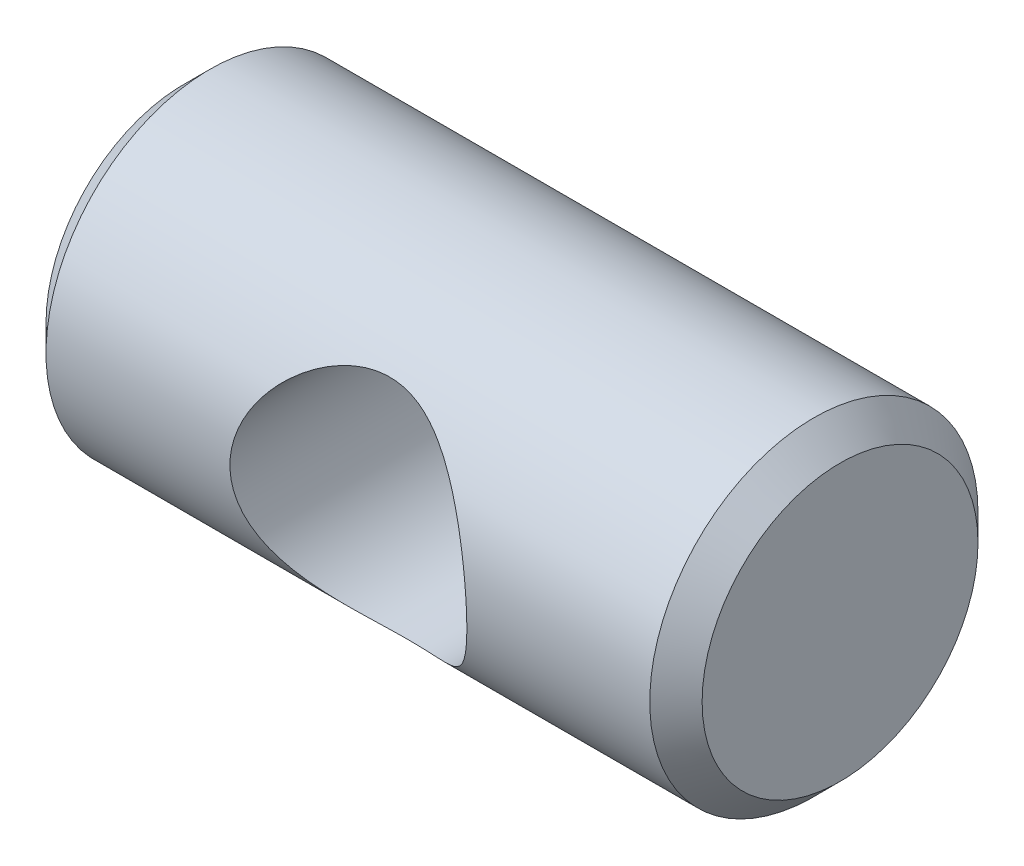
SolidWorks part; units mm, degrees
ref_plane "Plan de face" through (0, 0, 0) normal (0, 0, 1) x (1, 0, 0)
ref_plane "Plan de dessus" through (0, 0, 0) normal (0, 1, 0) x (1, 0, 0)
ref_plane "Plan de droite" through (0, 0, 0) normal (1, 0, 0) x (0, 0, -1)
sketch "Esquisse1" plane through (0, 0, 0) normal (1, 0, 0) x (0, 0, -1)
  circle A0 centre (0, 0) radius 4.765
  dimension "D1" = 9.53
extrude "Boss.-Extru.1" add sketch "Esquisse1" along normal mid plane 19.05
chamfer "Chanfrein1" distance 0.76 angle 45 2 edges at (-9.525, 0, -4.765) (9.525, 0, -4.765)
sketch "Esquisse2" plane through (0, 0, 0) normal (0, 0, 1) x (1, 0, 0)
  circle A0 centre (0, -0.25) radius 3.43
  dimension "D1" = 6.86
  dimension "D2" = 0.25
extrude "Enlèv. mat.-Extru.1" cut sketch "Esquisse2" against normal mid plane 19.05
